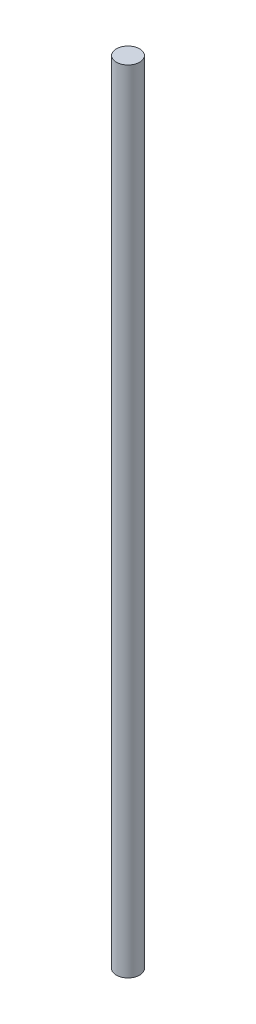
SolidWorks part; units mm, degrees
ref_plane "Front Plane" through (0, 0, 0) normal (0, 0, 1) x (1, 0, 0)
ref_plane "Top Plane" through (0, 0, 0) normal (0, 1, 0) x (1, 0, 0)
ref_plane "Right Plane" through (0, 0, 0) normal (1, 0, 0) x (0, 0, -1)
sketch "Sketch1" plane through (0, 0, 0) normal (0, 1, 0) x (1, 0, 0)
  circle A0 centre (0, 0) radius 5
  dimension "D1" = 10
extrude "Boss-Extrude1" add sketch "Sketch1" along normal blind 340
